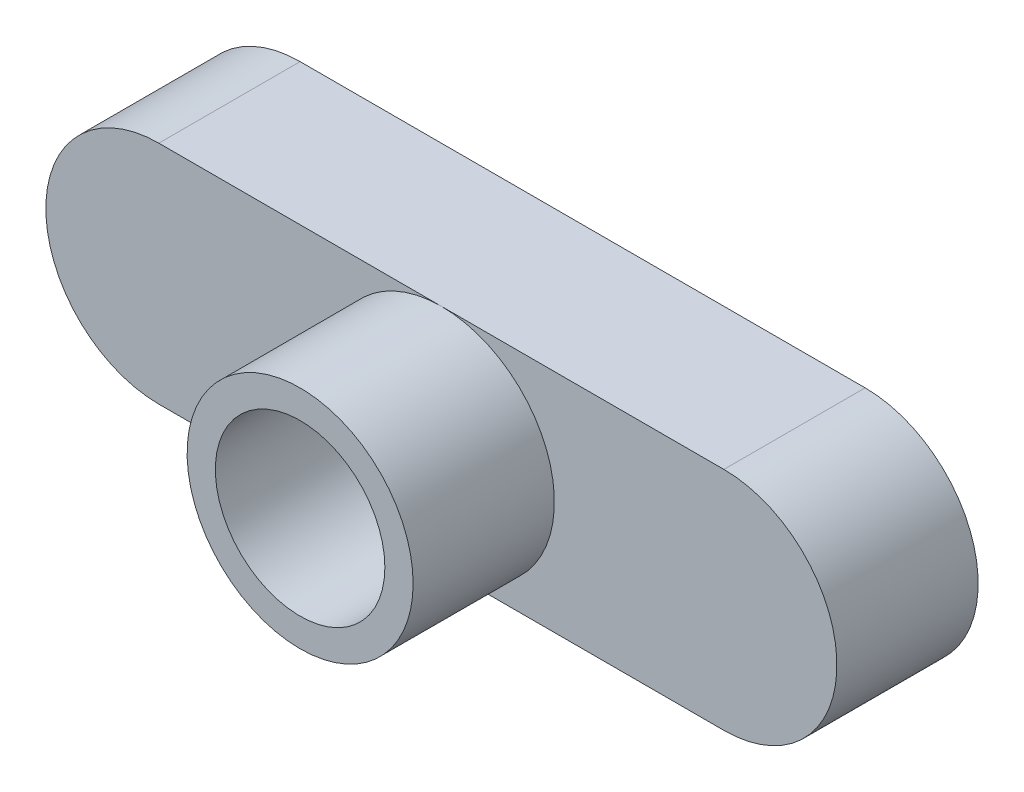
SolidWorks part; units mm, degrees
ref_plane "Front Plane" through (0, 0, 0) normal (0, 0, 1) x (1, 0, 0)
ref_plane "Top Plane" through (0, 0, 0) normal (0, 1, 0) x (1, 0, 0)
ref_plane "Right Plane" through (0, 0, 0) normal (1, 0, 0) x (0, 0, -1)
sketch "Sketch1" plane through (0, 0, 0) normal (0, 0, 1) x (1, 0, 0)
  line L0 (0, -4) -> (0, 4) construction
  line L1 (-10, 0) -> (10, 0) construction
  line L2 (-10, 4) -> (10, 4)
  line L3 (10, -4) -> (-10, -4)
  circle A0 centre (0, 0) radius 3
  arc A1 (10, -4) -> (10, 4) centre (10, 0) ccw
  arc A2 (-10, 4) -> (-10, -4) centre (-10, 0) ccw
  point P6 (0, 0)
  point P9 (0, 0)
  point P13 (0, 4)
  point P17 (0, -4)
  dimension "D1" = 6
  dimension "D4" = 8
  dimension "D5" = 8
  dimension "D2" = 8
  dimension "D3" = 20
extrude "Boss-Extrude1" add sketch "Sketch1" along normal blind 5
sketch "Sketch2" plane through (0, 0, 5) normal (0, 0, 1) x (1, 0, 0)
  circle A0 centre (0, 0) radius 3
  circle A1 centre (0, 0) radius 4
extrude "Boss-Extrude2" add sketch "Sketch2" along normal blind 5
